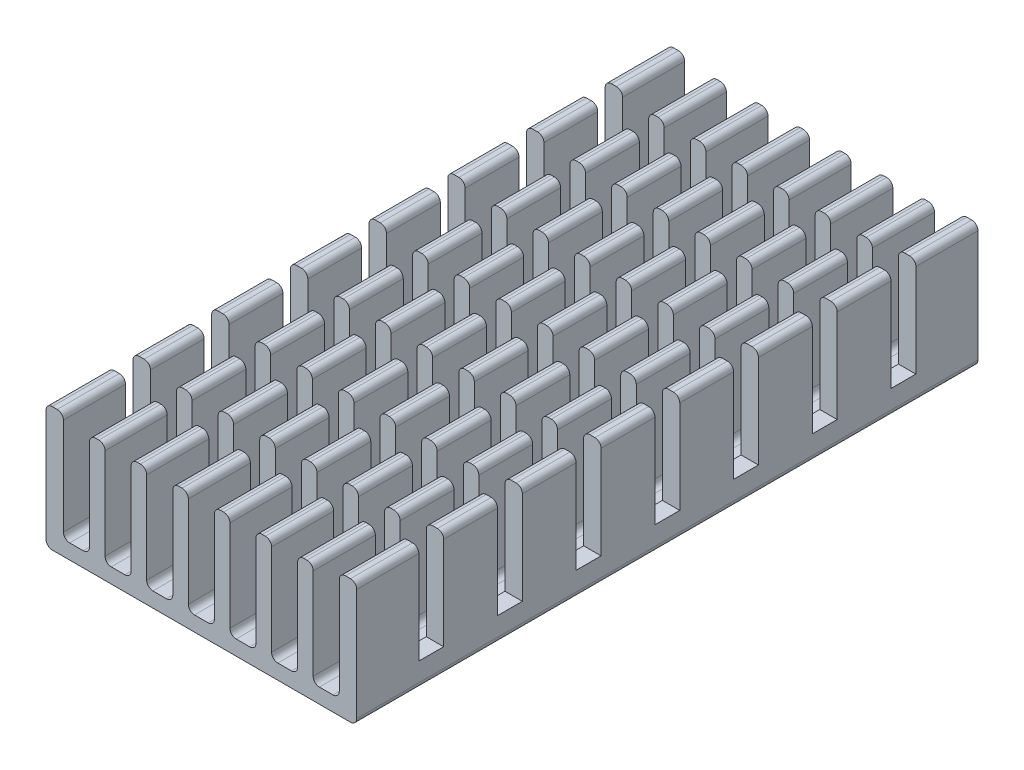
SolidWorks part; units mm, degrees
ref_plane "Front Plane" through (0, 0, 0) normal (0, 0, 1) x (1, 0, 0)
ref_plane "Top Plane" through (0, 0, 0) normal (0, 1, 0) x (1, 0, 0)
ref_plane "Right Plane" through (0, 0, 0) normal (1, 0, 0) x (0, 0, -1)
sketch "Sketch1" plane through (0, 0, 0) normal (0, 0, 1) x (1, 0, 0)
  line L0 (0, 0) -> (0, 10)
  line L1 (0, 10) -> (1.4, 10)
  line L2 (1.4, 10) -> (1.4, 1.2)
  line L3 (1.4, 1.2) -> (3.5, 1.2)
  line L4 (3.5, 1.2) -> (3.5, 9.5394)
  line L5 (3.5, 9.5394) -> (4.75, 9.5394)
  line L6 (4.75, 9.5394) -> (4.75, 1.2)
  line L7 (4.75, 1.2) -> (6.85, 1.2)
  line L8 (6.85, 1.2) -> (6.85, 9.5394)
  line L9 (6.85, 9.5394) -> (8.1, 9.5394)
  line L10 (8.1, 9.5394) -> (8.1, 1.2)
  line L11 (8.1, 1.2) -> (10.2, 1.2)
  line L12 (0, 0) -> (25, 0)
  line L13 (10.2, 1.2) -> (10.2, 9.5394)
  line L14 (10.2, 9.5394) -> (11.45, 9.5394)
  line L15 (11.45, 9.5394) -> (11.45, 1.2)
  line L16 (11.45, 1.2) -> (13.55, 1.2)
  line L17 (12.5, 0) -> (12.5, 10.6835) construction
  line L18 (13.55, 9.5394) -> (13.55, 1.2)
  line L19 (14.8, 9.5394) -> (13.55, 9.5394)
  line L20 (14.8, 1.2) -> (14.8, 9.5394)
  line L21 (16.9, 1.2) -> (14.8, 1.2)
  line L22 (20.25, 1.2) -> (18.15, 1.2)
  line L23 (16.9, 9.5394) -> (16.9, 1.2)
  line L24 (18.15, 1.2) -> (18.15, 9.5394)
  line L25 (18.15, 9.5394) -> (16.9, 9.5394)
  line L26 (21.5, 9.5394) -> (20.25, 9.5394)
  line L27 (20.25, 9.5394) -> (20.25, 1.2)
  line L28 (21.5, 1.2) -> (21.5, 9.5394)
  line L29 (23.6, 1.2) -> (21.5, 1.2)
  line L30 (23.6, 10) -> (23.6, 1.2)
  line L31 (25, 10) -> (23.6, 10)
  line L32 (25, 0) -> (25, 10)
  point P20 (12.5, 1.2)
  dimension "D1" = 10
  dimension "D2" = 1.4
  dimension "D3" = 1.25
  dimension "D4" = 1.2
  dimension "D5" = 2.1
  dimension "D6" = 2.1
  dimension "D7" = 1.25
  dimension "D8" = 2.1
  dimension "D9" = 1.25
  dimension "D11" = 12.5
extrude "Boss-Extrude1" add sketch "Sketch1" along normal blind 50
fillet "Fillet1" radius 0.5 32 edges at (25, 10, 25) (23.6, 10, 25) (21.5, 9.5394, 25) (20.25, 9.5394, 25) (18.15, 9.5394, 25) (16.9, 9.5394, 25) (14.8, 9.5394, 25) (13.55, 9.5394, 25) (11.45, 9.5394, 25) (10.2, 9.5394, 25) (8.1, 9.5394, 25) (6.85, 9.5394, 25) (23.6, 1.2, 25) (21.5, 1.2, 25) (20.25, 1.2, 25) (18.15, 1.2, 25) (16.9, 1.2, 25) (14.8, 1.2, 25) (13.55, 1.2, 25) (11.45, 1.2, 25) (10.2, 1.2, 25) (8.1, 1.2, 25) (6.85, 1.2, 25) (4.75, 1.2, 25) (3.5, 1.2, 25) (4.75, 9.5394, 25) (3.5, 9.5394, 25) (1.4, 1.2, 25) (1.4, 10, 25) (0, 10, 25) (25, 0, 25) (0, 0, 25)
sketch "Sketch2" plane through (25, 0, 0) normal (1, 0, 0) x (0, 0, -1)
  line L0 (-7, 10) -> (-5, 10)
  line L1 (-50, 10) -> (0, 10) construction
  line L2 (-5, 10) -> (-5, 2.0093)
  line L3 (-5, 2.0093) -> (-7, 2.0093)
  line L4 (-7, 2.0093) -> (-7, 10)
  line L5 (0, 0.5) -> (0, 9.5) construction
  line L6 (-13.3333, 2.0093) -> (-13.3333, 10)
  line L7 (-13.3333, 10) -> (-11.3333, 10)
  line L8 (-11.3333, 10) -> (-11.3333, 2.0093)
  line L9 (-11.3333, 2.0093) -> (-13.3333, 2.0093)
  line L10 (-19.6667, 2.0093) -> (-19.6667, 10)
  line L11 (-19.6667, 10) -> (-17.6667, 10)
  line L12 (-17.6667, 10) -> (-17.6667, 2.0093)
  line L13 (-17.6667, 2.0093) -> (-19.6667, 2.0093)
  line L14 (-26, 2.0093) -> (-26, 10)
  line L15 (-26, 10) -> (-24, 10)
  line L16 (-24, 10) -> (-24, 2.0093)
  line L17 (-24, 2.0093) -> (-26, 2.0093)
  line L18 (-32.3333, 2.0093) -> (-32.3333, 10)
  line L19 (-32.3333, 10) -> (-30.3333, 10)
  line L20 (-30.3333, 10) -> (-30.3333, 2.0093)
  line L21 (-30.3333, 2.0093) -> (-32.3333, 2.0093)
  line L22 (-38.6667, 2.0093) -> (-38.6667, 10)
  line L23 (-38.6667, 10) -> (-36.6667, 10)
  line L24 (-36.6667, 10) -> (-36.6667, 2.0093)
  line L25 (-36.6667, 2.0093) -> (-38.6667, 2.0093)
  line L26 (-45, 2.0093) -> (-45, 10)
  line L27 (-45, 10) -> (-43, 10)
  line L28 (-43, 10) -> (-43, 2.0093)
  line L29 (-43, 2.0093) -> (-45, 2.0093)
  line L30 (-50, 0.5) -> (-50, 9.5) construction
  dimension "D1" = 2
  dimension "D2" = 5
  dimension "D3" = 7
  dimension "D4" = 5
extrude "Cut-Extrude1" cut sketch "Sketch2" against normal through all
